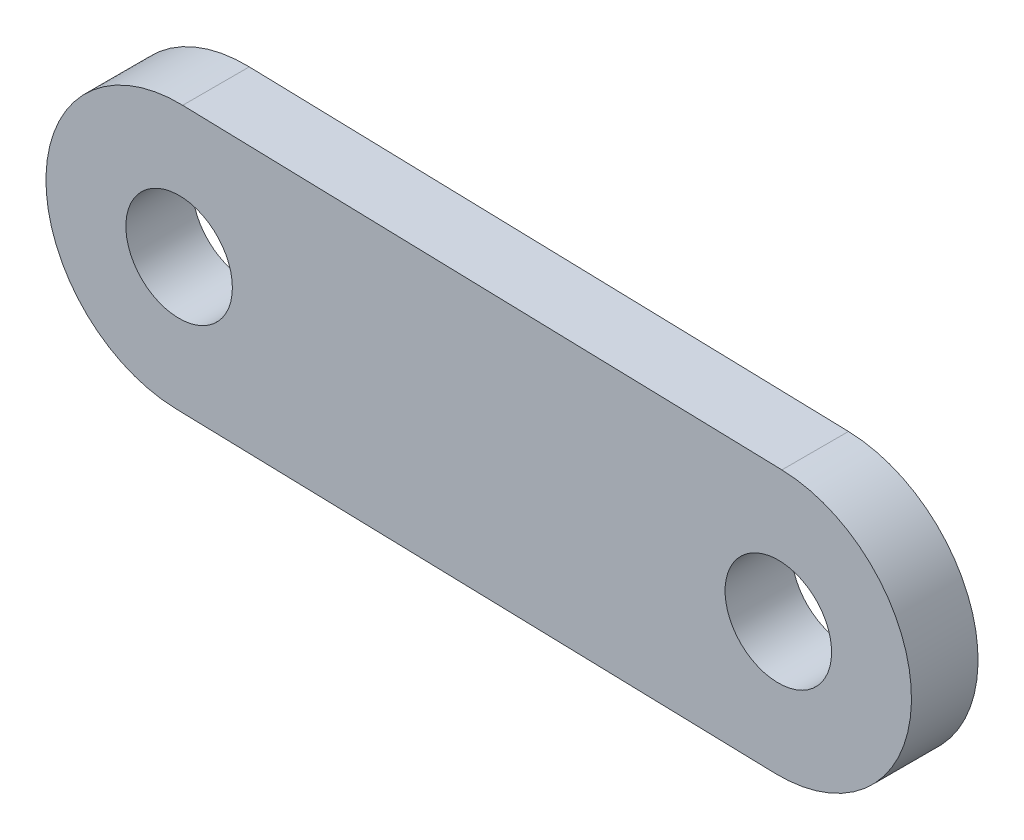
SolidWorks part; units mm, degrees
ref_plane "Front Plane" through (0, 0, 0) normal (0, 0, 1) x (1, 0, 0)
ref_plane "Top Plane" through (0, 0, 0) normal (0, 1, 0) x (1, 0, 0)
ref_plane "Right Plane" through (0, 0, 0) normal (1, 0, 0) x (0, 0, -1)
sketch "Sketch1" plane through (0, 0, 0) normal (0, 0, 1) x (1, 0, 0)
  line L0 (-22.5, 0.6061) -> (22.5, -0.6061) construction
  line L1 (-22.2307, 10.6025) -> (22.7693, 9.3903)
  line L2 (-22.7693, -9.3903) -> (22.2307, -10.6025)
  arc A0 (-22.2307, 10.6025) -> (-22.7693, -9.3903) centre (-22.5, 0.6061) ccw
  arc A1 (22.2307, -10.6025) -> (22.7693, 9.3903) centre (22.5, -0.6061) ccw
  circle A2 centre (22.5, -0.6061) radius 4
  circle A3 centre (-22.5, 0.6061) radius 4
  point P2 (0, 0)
  dimension "D3" = 8
  dimension "D4" = 8
  dimension "D1" = 45
  dimension "D2" = 20
extrude "Boss-Extrude1" add sketch "Sketch1" along normal blind 5
